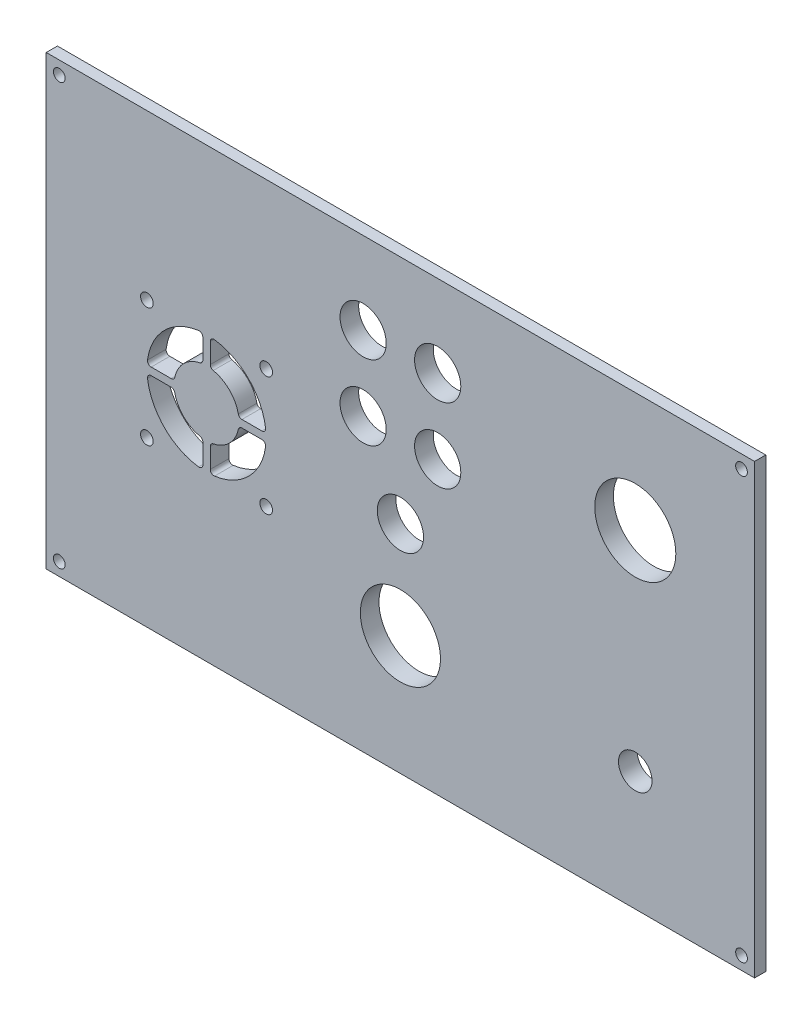
SolidWorks part; units mm, degrees
ref_plane "Front Plane" through (0, 0, 0) normal (0, 0, 1) x (1, 0, 0)
ref_plane "Top Plane" through (0, 0, 0) normal (0, 1, 0) x (1, 0, 0)
ref_plane "Right Plane" through (0, 0, 0) normal (1, 0, 0) x (0, 0, -1)
sketch "Sketch1" plane through (0, 0, 0) normal (0, 0, 1) x (1, 0, 0)
  line L0 (-10, 38) -> (10, 38) construction
  line L1 (-95, -60) -> (95, -60)
  line L2 (-95, -60) -> (-95, 60)
  line L3 (-95, 60) -> (95, 60)
  line L4 (95, -60) -> (95, 60)
  line L5 (-95, -60) -> (95, 60) construction
  line L6 (-95, 60) -> (95, -60) construction
  line L7 (10, 38) -> (10, 18) construction
  line L8 (-95, 0) -> (95, 0) construction
  line L9 (10, 18) -> (-10, 18) construction
  line L10 (-21, 47.4067) -> (-83, 47.4067) construction
  line L11 (-21, 47.4067) -> (-21, -56.5933) construction
  line L12 (-21, -56.5933) -> (-83, -56.5933) construction
  line L13 (-83, 47.4067) -> (-83, -56.5933) construction
  line L14 (-10, 18) -> (-10, 38) construction
  line L15 (-52, 47.4067) -> (-52, -56.5933) construction
  line L16 (-68, -16) -> (-36, -16) construction
  line L17 (-68, -16) -> (-68, 16) construction
  line L18 (-68, 16) -> (-36, 16) construction
  line L19 (-36, -16) -> (-36, 16) construction
  line L20 (-53, 8.6454) -> (-53, 15.9543)
  line L21 (-51, 8.6454) -> (-51, 15.9543)
  line L22 (-43.3546, 1) -> (-36.0457, 1)
  line L23 (-43.3546, -1) -> (-36.0457, -1)
  line L24 (-51, -8.6454) -> (-51, -15.9543)
  line L25 (-53, -8.6454) -> (-53, -15.9543)
  line L26 (-60.6454, -1) -> (-67.9543, -1)
  line L27 (-60.6454, 1) -> (-67.9543, 1)
  line L46 (0, 18) -> (0, -2) construction
  circle A0 centre (-91.5, 56.5) radius 1.575
  circle A1 centre (91.5, 56.5) radius 1.575
  circle A2 centre (91.5, -56.5) radius 1.575
  circle A3 centre (-91.5, -56.5) radius 1.575
  circle A13 centre (-36, 16) radius 1.7
  circle A14 centre (-36, -16) radius 1.7
  circle A15 centre (-68, -16) radius 1.7
  circle A16 centre (-68, 16) radius 1.7
  arc A17 (-67.9543, -1) -> (-53, -15.9543) centre (-52, 0) ccw
  arc A18 (-60.6454, -1) -> (-53, -8.6454) centre (-52, 0) ccw
  arc A19 (-53, 8.6454) -> (-60.6454, 1) centre (-52, 0) ccw
  arc A20 (-53, 15.9543) -> (-67.9543, 1) centre (-52, 0) ccw
  arc A21 (-43.3546, 1) -> (-51, 8.6454) centre (-52, 0) ccw
  arc A22 (-36.0457, 1) -> (-51, 15.9543) centre (-52, 0) ccw
  arc A23 (-51, -8.6454) -> (-43.3546, -1) centre (-52, 0) ccw
  arc A24 (-51, -15.9543) -> (-36.0457, -1) centre (-52, 0) ccw
  circle A26 centre (63, 28) radius 30 construction
  circle A27 centre (63, 28) radius 10.875
  circle A28 centre (0, -28) radius 10.75
  circle A29 centre (63, -28) radius 4.5
  circle A30 centre (63, -28) radius 21 construction
  circle A31 centre (-10, 38) radius 6.2
  circle A32 centre (10, 18) radius 6.2
  circle A33 centre (0, -2) radius 6.2
  circle A35 centre (-10, 18) radius 6.2
  circle A36 centre (10, 38) radius 6.2
  point P0 (0, 0)
  point P47 (-52, 16)
  point P52 (-36, 0)
  point P75 (-52, 0)
  point P79 (10, 28)
  dimension "D3" = 3.15
  dimension "D4" = 3.5
  dimension "D5" = 3.5
  dimension "D8" = 3.5
  dimension "D9" = 3.5
  dimension "D10" = 3.5
  dimension "D11" = 60
  dimension "D12" = 21.75
  dimension "D15" = 21.5
  dimension "D16" = 9
  dimension "D17" = 42
  dimension "D18" = 12.4
  dimension "D19" = 20
  dimension "D22" = 3.4
  dimension "D26" = 20
  dimension "D1" = 190
  dimension "D2" = 120
  dimension "D13" = 62
  dimension "D14" = 104
  dimension "D20" = 32
  dimension "D21" = 12
  dimension "D23" = 2
  dimension "D25" = 20
  dimension "D27" = 32
  dimension "D28" = 32
  dimension "D29" = 32
  dimension "D6" = 2
  dimension "D7" = 2
  dimension "D24" = 4
extrude "Boss-Extrude1" add sketch "Sketch1" along normal blind 5
sketch "Sketch5" plane through (0, 0, 0) normal (0, 0, 1) x (1, 0, 0)
  line L1 (-95, 60) -> (95, 60)
  line L2 (-95, 60) -> (-95, -60)
  line L3 (-95, -60) -> (95, -60)
  line L4 (95, 60) -> (95, -60)
  line L38 (-87.5, 57.5) -> (87.5, 57.5)
  line L39 (87.5, 57.5) -> (87.5, 52.5)
  line L40 (92.5, 52.5) -> (87.5, 52.5)
  line L41 (92.5, 52.5) -> (92.5, -52.5)
  line L42 (92.5, -52.5) -> (87.5, -52.5)
  line L43 (87.5, -57.5) -> (87.5, -52.5)
  line L44 (-87.5, -57.5) -> (87.5, -57.5)
  line L45 (-87.5, -57.5) -> (-87.5, -52.5)
  line L46 (-92.5, -52.5) -> (-87.5, -52.5)
  line L47 (-92.5, 52.5) -> (-92.5, -52.5)
  line L48 (-92.5, 52.5) -> (-87.5, 52.5)
  line L49 (-87.5, 57.5) -> (-87.5, 52.5)
  dimension "D2" = 190
extrude "Cut-Extrude3" cut sketch "Sketch5" against normal blind 1 and the other way blind 2
fillet "Fillet1" radius 1 16 edges at (-51, -15.9543, 2.5) (-53, 8.6454, 2.5) (-67.9543, 1, 2.5) (-36.0457, -1, 2.5) (-43.3546, -1, 2.5) (-51, -8.6454, 2.5) (-53, -8.6454, 2.5) (-60.6454, -1, 2.5) (-60.6454, 1, 2.5) (-53, -15.9543, 2.5) (-36.0457, 1, 2.5) (-43.3546, 1, 2.5) (-51, 8.6454, 2.5) (-51, 15.9543, 2.5) (-53, 15.9543, 2.5) (-67.9543, -1, 2.5)
sketch "Sketch6" plane through (0, 0, 0) normal (0, 0, -1) x (-1, 0, 0)
  circle A0 centre (-72.6, -28) radius 1.875
  circle A1 centre (-63, -28) radius 4.5 construction
  circle A2 centre (-63, -28) radius 4.5 construction
  dimension "D1" = 3.75
  dimension "D2" = 9.6
extrude "Cut-Extrude4" cut sketch "Sketch6" against normal blind 2.5
